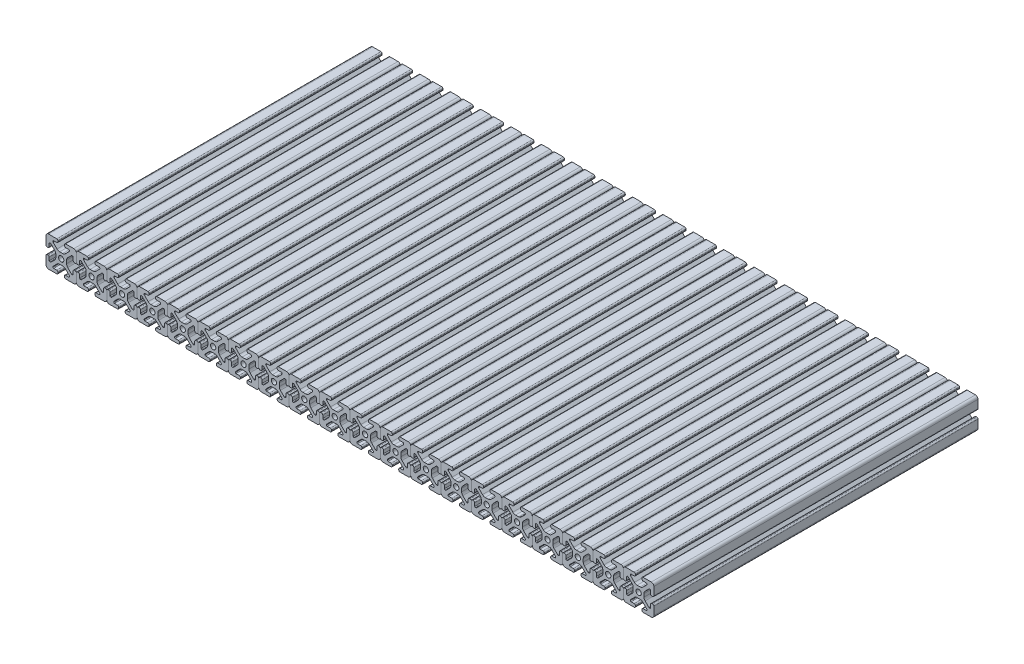
SolidWorks part; units mm, degrees
ref_plane "Front Plane" through (0, 0, 0) normal (0, 0, 1) x (1, 0, 0)
ref_plane "Top Plane" through (0, 0, 0) normal (0, 1, 0) x (1, 0, 0)
ref_plane "Right Plane" through (0, 0, 0) normal (1, 0, 0) x (0, 0, -1)
sketch "Sketch1" plane through (0, 0, 0) normal (0, 0, 1) x (1, 0, 0)
  line L0 (0, 0) -> (-361.95, 0) construction
  point P3 (0, 0)
  line B0 (-366.014, 16.5396) -> (-366.014, 17.4964)
  line B1 (-367.5676, 19.05) -> (-377.7975, 19.05)
  line B2 (-381, 15.8475) -> (-381, 5.6176)
  line B3 (-379.4464, 4.064) -> (-378.4896, 4.064)
  line B4 (-376.936, 5.6176) -> (-376.936, 9.3853)
  line B5 (-376.0343, 10.287) -> (-375.466, 10.287)
  line B6 (-374.8284, 10.0229) -> (-370.0976, 5.2921)
  line B7 (-368.7064, 1.9335) -> (-368.7064, -1.9335)
  line B8 (-370.0976, -5.2921) -> (-374.8284, -10.0229)
  line B9 (-375.466, -10.287) -> (-376.0343, -10.287)
  line B10 (-376.936, -9.3853) -> (-376.936, -5.6176)
  line B11 (-378.4896, -4.064) -> (-379.4464, -4.064)
  line B12 (-381, -5.6176) -> (-381, -15.8475)
  line B13 (-377.7975, -19.05) -> (-367.5676, -19.05)
  line B14 (-366.014, -17.4964) -> (-366.014, -16.5396)
  line B15 (-367.5676, -14.986) -> (-371.3353, -14.986)
  line B16 (-372.237, -14.0843) -> (-372.237, -13.5524)
  line B17 (-371.9729, -12.9148) -> (-367.2022, -8.144)
  line B18 (-363.8522, -6.7564) -> (-360.0478, -6.7564)
  line B19 (-356.6978, -8.144) -> (-351.9271, -12.9148)
  line B20 (-351.663, -13.5524) -> (-351.663, -14.0843)
  line B21 (-352.5647, -14.986) -> (-356.3324, -14.986)
  line B22 (-357.886, -16.5396) -> (-357.886, -17.4964)
  line B23 (-356.3324, -19.05) -> (-346.1025, -19.05)
  line B24 (-342.9, -15.8475) -> (-342.9, -5.6176)
  line B25 (-344.4536, -4.064) -> (-345.4104, -4.064)
  line B26 (-346.964, -5.6176) -> (-346.964, -9.3853)
  line B27 (-347.8657, -10.287) -> (-348.434, -10.287)
  line B28 (-349.0716, -10.0229) -> (-353.8024, -5.2921)
  line B29 (-355.1936, -1.9335) -> (-355.1936, 1.9335)
  line B30 (-353.8024, 5.2921) -> (-349.0716, 10.0229)
  line B31 (-348.434, 10.287) -> (-347.8657, 10.287)
  line B32 (-346.964, 9.3853) -> (-346.964, 5.6176)
  line B33 (-345.4104, 4.064) -> (-344.4536, 4.064)
  line B34 (-342.9, 5.6176) -> (-342.9, 15.8475)
  line B35 (-346.1025, 19.05) -> (-356.3324, 19.05)
  line B36 (-357.886, 17.4964) -> (-357.886, 16.5396)
  line B37 (-356.3324, 14.986) -> (-352.5647, 14.986)
  line B38 (-351.663, 14.0843) -> (-351.663, 13.5524)
  line B39 (-351.9271, 12.9148) -> (-356.6978, 8.144)
  line B40 (-360.0478, 6.7564) -> (-363.8522, 6.7564)
  line B41 (-367.2022, 8.144) -> (-371.9729, 12.9148)
  line B42 (-372.237, 13.5524) -> (-372.237, 14.0843)
  line B43 (-371.3353, 14.986) -> (-367.5676, 14.986)
  arc B44 (-367.5676, 14.986) -> (-366.014, 16.5396) centre (-367.5676, 16.5396) ccw
  arc B45 (-366.014, 17.4964) -> (-367.5676, 19.05) centre (-367.5676, 17.4964) ccw
  arc B46 (-377.7975, 19.05) -> (-381, 15.8475) centre (-377.8251, 15.8751) ccw
  arc B47 (-381, 5.6176) -> (-379.4464, 4.064) centre (-379.4464, 5.6176) ccw
  arc B48 (-378.4896, 4.064) -> (-376.936, 5.6176) centre (-378.4896, 5.6176) ccw
  arc B49 (-376.0343, 10.287) -> (-376.936, 9.3853) centre (-376.0343, 9.3853) ccw
  arc B50 (-374.8284, 10.0229) -> (-375.466, 10.287) centre (-375.466, 9.3853) ccw
  arc B51 (-368.7064, 1.9335) -> (-370.0976, 5.2921) centre (-373.4562, 1.9335) ccw
  arc B52 (-370.0976, -5.2921) -> (-368.7064, -1.9335) centre (-373.4562, -1.9335) ccw
  arc B53 (-375.466, -10.287) -> (-374.8284, -10.0229) centre (-375.466, -9.3853) ccw
  arc B54 (-376.936, -9.3853) -> (-376.0343, -10.287) centre (-376.0343, -9.3853) ccw
  arc B55 (-376.936, -5.6176) -> (-378.4896, -4.064) centre (-378.4896, -5.6176) ccw
  arc B56 (-379.4464, -4.064) -> (-381, -5.6176) centre (-379.4464, -5.6176) ccw
  arc B57 (-381, -15.8475) -> (-377.7975, -19.05) centre (-377.8251, -15.8751) ccw
  arc B58 (-367.5676, -19.05) -> (-366.014, -17.4964) centre (-367.5676, -17.4964) ccw
  arc B59 (-366.014, -16.5396) -> (-367.5676, -14.986) centre (-367.5676, -16.5396) ccw
  arc B60 (-372.237, -14.0843) -> (-371.3353, -14.986) centre (-371.3353, -14.0843) ccw
  arc B61 (-371.9729, -12.9148) -> (-372.237, -13.5524) centre (-371.3353, -13.5524) ccw
  arc B62 (-363.8522, -6.7564) -> (-367.2022, -8.144) centre (-363.8522, -11.494) ccw
  arc B63 (-356.6978, -8.144) -> (-360.0478, -6.7564) centre (-360.0478, -11.494) ccw
  arc B64 (-351.663, -13.5524) -> (-351.9271, -12.9148) centre (-352.5647, -13.5524) ccw
  arc B65 (-352.5647, -14.986) -> (-351.663, -14.0843) centre (-352.5647, -14.0843) ccw
  arc B66 (-356.3324, -14.986) -> (-357.886, -16.5396) centre (-356.3324, -16.5396) ccw
  arc B67 (-357.886, -17.4964) -> (-356.3324, -19.05) centre (-356.3324, -17.4964) ccw
  arc B68 (-346.1025, -19.05) -> (-342.9, -15.8475) centre (-346.0749, -15.8751) ccw
  arc B69 (-342.9, -5.6176) -> (-344.4536, -4.064) centre (-344.4536, -5.6176) ccw
  arc B70 (-345.4104, -4.064) -> (-346.964, -5.6176) centre (-345.4104, -5.6176) ccw
  arc B71 (-347.8657, -10.287) -> (-346.964, -9.3853) centre (-347.8657, -9.3853) ccw
  arc B72 (-349.0716, -10.0229) -> (-348.434, -10.287) centre (-348.434, -9.3853) ccw
  arc B73 (-355.1936, -1.9335) -> (-353.8024, -5.2921) centre (-350.4438, -1.9335) ccw
  arc B74 (-353.8024, 5.2921) -> (-355.1936, 1.9335) centre (-350.4438, 1.9335) ccw
  arc B75 (-348.434, 10.287) -> (-349.0716, 10.0229) centre (-348.434, 9.3853) ccw
  arc B76 (-346.964, 9.3853) -> (-347.8657, 10.287) centre (-347.8657, 9.3853) ccw
  arc B77 (-346.964, 5.6176) -> (-345.4104, 4.064) centre (-345.4104, 5.6176) ccw
  arc B78 (-344.4536, 4.064) -> (-342.9, 5.6176) centre (-344.4536, 5.6176) ccw
  arc B79 (-342.9, 15.8475) -> (-346.1025, 19.05) centre (-346.0749, 15.8751) ccw
  arc B80 (-356.3324, 19.05) -> (-357.886, 17.4964) centre (-356.3324, 17.4964) ccw
  arc B81 (-357.886, 16.5396) -> (-356.3324, 14.986) centre (-356.3324, 16.5396) ccw
  arc B82 (-351.663, 14.0843) -> (-352.5647, 14.986) centre (-352.5647, 14.0843) ccw
  arc B83 (-351.9271, 12.9148) -> (-351.663, 13.5524) centre (-352.5647, 13.5524) ccw
  arc B84 (-360.0478, 6.7564) -> (-356.6978, 8.144) centre (-360.0478, 11.494) ccw
  arc B85 (-367.2022, 8.144) -> (-363.8522, 6.7564) centre (-363.8522, 11.494) ccw
  arc B86 (-372.237, 13.5524) -> (-371.9729, 12.9148) centre (-371.3353, 13.5524) ccw
  arc B87 (-371.3353, 14.986) -> (-372.237, 14.0843) centre (-371.3353, 14.0843) ccw
  circle B88 centre (-361.95, 0) radius 3.3274
  dimension "D1" = 361.95
sketch_block_instance "Block1-1"
sketch_block "Block1"
extrude "Boss-Extrude1" add sketch "Sketch1" along normal mid plane 406.4
pattern_linear "LPattern1" count 20 spacing 38.1 along (1, 0, 0) of bodies 101
